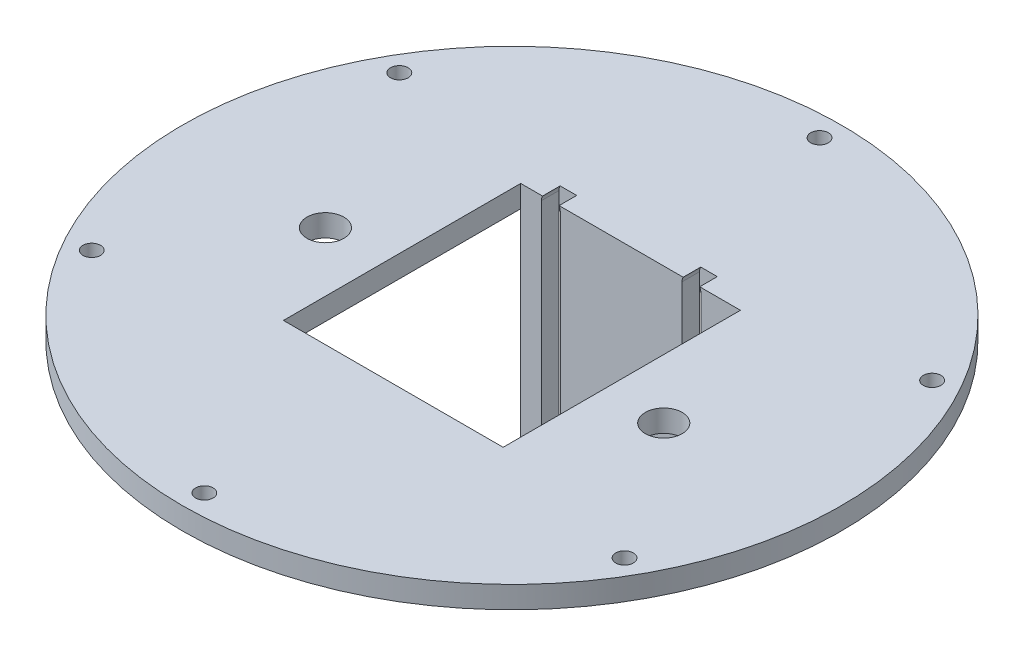
SolidWorks part; units mm, degrees
ref_plane "Front Plane" through (0, 0, 0) normal (0, 0, 1) x (1, 0, 0)
ref_plane "Top Plane" through (0, 0, 0) normal (0, 1, 0) x (1, 0, 0)
ref_plane "Right Plane" through (0, 0, 0) normal (1, 0, 0) x (0, 0, -1)
sketch "Sketch1" plane through (0, 0, 0) normal (0, 1, 0) x (1, 0, 0)
  line L0 (0, 0) -> (0, -35167.8801) construction
  line L1 (0, 0) -> (35167.8801, 0) construction
  line L3 (100, -50) -> (-100, -50)
  line L4 (100, -50) -> (100, 50)
  line L5 (100, 50) -> (-100, 50)
  line L6 (-100, -50) -> (-100, 50)
  line L7 (100, -50) -> (-100, 50) construction
  line L8 (100, 50) -> (-100, -50) construction
  point P5 (0, 0)
  dimension "D1" = 100
  dimension "D2" = 200
extrude "Boss-Extrude1" add sketch "Sketch1" along normal blind 5
sketch "Sketch2" plane through (0, 5, 0) normal (0, 1, 0) x (1, 0, 0)
  line L1 (5, 27) -> (55, 27)
  line L2 (5, 27) -> (5, -27)
  line L3 (5, -27) -> (55, -27)
  line L4 (55, 27) -> (55, -27)
  line L5 (100, -50) -> (100, 50) construction
  line L6 (100, 50) -> (-100, 50) construction
  dimension "D1" = 23
  dimension "D2" = 50
  dimension "D3" = 54
  dimension "D4" = 45
extrude "Cut-Extrude1" cut sketch "Sketch2" against normal through all
sketch "Sketch3" plane through (0, 0, 0) normal (0, -1, 0) x (1, 0, 0)
  line L1 (5, -27) -> (55, -27)
  line L2 (5, -27) -> (5, -31)
  line L3 (5, -31) -> (55, -31)
  line L4 (55, -27) -> (55, -31)
  dimension "D1" = 4
extrude "Boss-Extrude2" add sketch "Sketch3" along normal blind 45
sketch "Sketch4" plane through (0, 0, -27) normal (0, 0, 1) x (1, 0, 0)
  line L0 (9.7, 3.9603) -> (9.7, -35.5714)
  line L1 (9.7, 3.9603) -> (9.7, -35.5714) construction
  line L2 (14, -35.5714) -> (14, 3.9603)
  line L3 (14, 3.9603) -> (14, -35.5714) construction
  line L4 (19.6987, -6.1966) -> (9.7, -6.1977)
  line L6 (41.7, -31.9492) -> (41.7, 3.9603)
  line L7 (46, 3.9603) -> (46, -31.9492)
  arc A0 (9.7, -35.5714) -> (14, -35.5714) centre (11.85, -35.5714) ccw
  arc A1 (14, 3.9603) -> (9.7, 3.9603) centre (11.85, 3.9603) ccw
  arc A5 (41.7, 3.9603) -> (46, 3.9603) centre (43.85, 3.9603) cw
  arc A6 (46, -31.9492) -> (41.7, -31.9492) centre (43.85, -31.9492) cw
  dimension "D1" = 2.15
extrude "Cut-Extrude3" cut sketch "Sketch4" against normal up to surface (4 mm away) contours L2 A1 L0 A0 | A6 L7 A5 L6
sketch "Sketch19" plane through (0, 0, -50) normal (0, 0, -1) x (-1, 0, 0)
  line L4 (-100, 0) -> (100, 0)
  line L5 (100, 0) -> (100, 5)
  line L6 (100, 5) -> (-100, 5)
  line L7 (-100, 5) -> (-100, 0)
  line L8 (-100, 0) -> (100, 0)
  line L9 (100, 0) -> (100, 5)
  line L10 (100, 5) -> (-100, 5)
  line L11 (-100, 5) -> (-100, 0)
  dimension "D1" = 0
extrude "Boss-Extrude3" add sketch "Sketch19" along normal blind 25
sketch "Sketch20" plane through (0, 0, 50) normal (0, 0, 1) x (1, 0, 0)
  line L4 (-100, 0) -> (100, 0)
  line L5 (100, 0) -> (100, 5)
  line L6 (100, 5) -> (-100, 5)
  line L7 (-100, 5) -> (-100, 0)
  line L8 (-100, 0) -> (100, 0)
  line L9 (100, 0) -> (100, 5)
  line L10 (100, 5) -> (-100, 5)
  line L11 (-100, 5) -> (-100, 0)
  dimension "D1" = 0
extrude "Boss-Extrude4" add sketch "Sketch20" along normal blind 25
sketch "Sketch21" plane through (100, 0, 0) normal (1, 0, 0) x (0, 0, -1)
  line L4 (-75, 0) -> (75, 0)
  line L5 (75, 0) -> (75, 5)
  line L6 (75, 5) -> (-75, 5)
  line L7 (-75, 5) -> (-75, 0)
  line L8 (-75, 0) -> (75, 0)
  line L9 (75, 0) -> (75, 5)
  line L10 (75, 5) -> (-75, 5)
  line L11 (-75, 5) -> (-75, 0)
  dimension "D1" = 0
extrude "Boss-Extrude5" add sketch "Sketch21" along normal blind 25
sketch "Sketch22" plane through (0, 5, 0) normal (0, 1, 0) x (1, 0, 0)
  line L3 (5, 0) -> (55, 0) construction
  line L4 (5, 27) -> (5, -27) construction
  line L5 (55, -27) -> (55, 27) construction
  circle A0 centre (30, 0) radius 75
  dimension "D1" = 150
extrude "Cut-Extrude6" cut sketch "Sketch22" against normal through all flip side to cut contours A0
sketch "Sketch26" plane through (0, 5, 0) normal (0, 1, 0) x (1, 0, 0)
  circle A0 centre (30, 0) radius 70 construction
  circle A1 centre (30, -70) radius 2
  circle A2 centre (-30.6218, -35) radius 2
  circle A3 centre (-30.6218, 35) radius 2
  circle A4 centre (30, 70) radius 2
  circle A5 centre (90.6218, 35) radius 2
  circle A6 centre (90.6218, -35) radius 2
  dimension "D1" = 140
  dimension "D2" = 4
  dimension "D3" = 6
extrude "Cut-Extrude7" cut sketch "Sketch26" against normal through all
sketch "Sketch28" plane through (0, 5, 0) normal (0, 1, 0) x (1, 0, 0)
  circle A0 centre (-8.5, -3.95) radius 4.2
  circle A1 centre (68.5, -3.95) radius 4.2
  dimension "D1" = 8.4
  dimension "D2" = 8.4
extrude "Cut-Extrude8" cut sketch "Sketch28" against normal up to next
sketch "Sketch30" plane through (0, 0, -27) normal (0, 0, 1) x (1, 0, 0)
  line L0 (14, -6.1973) -> (14, -40.5714)
  line L1 (9.7, -40.5714) -> (9.7, -6.1977)
  line L2 (9.7, -6.1977) -> (14, -6.1973)
  line L3 (41.7, -31.9492) -> (41.7, -36.9492)
  line L4 (46, -36.9492) -> (46, -31.9492)
  line L5 (46, -31.9492) -> (41.7, -31.9492)
  arc A0 (14, -40.5714) -> (9.7, -40.5714) centre (11.85, -40.5714) cw
  arc A1 (41.7, -36.9492) -> (46, -36.9492) centre (43.85, -36.9492) ccw
extrude "Cut-Extrude10" cut sketch "Sketch30" against normal up to surface (4 mm away) up to face at (28.5667, -14.037, -31)
